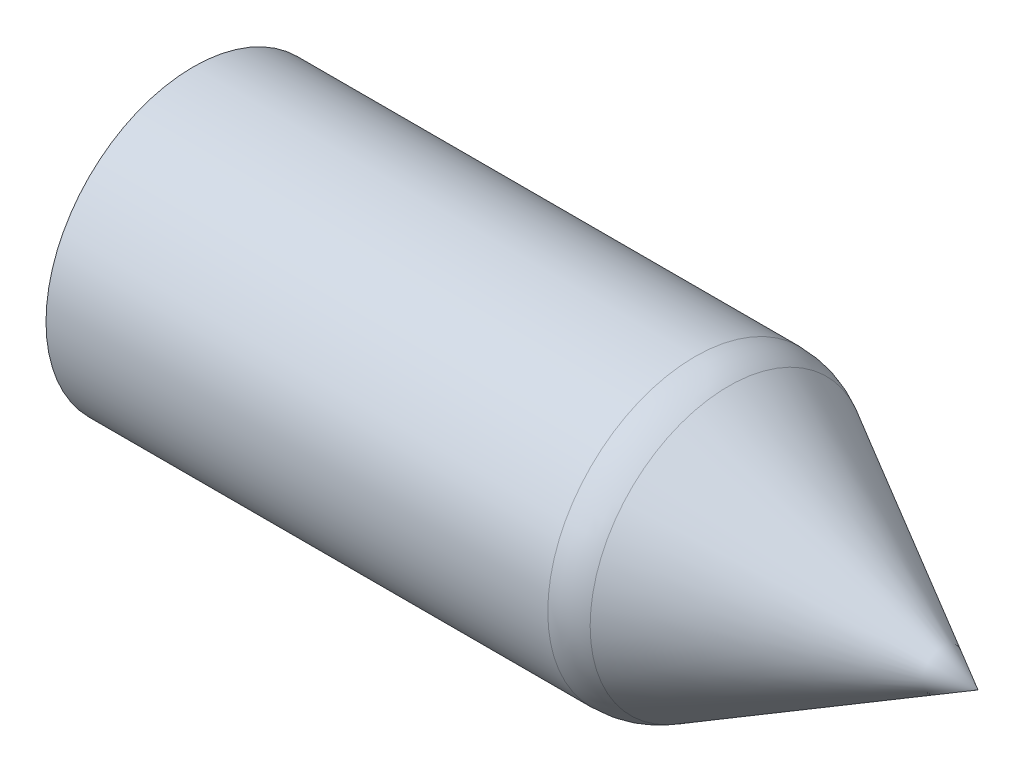
SolidWorks part; units mm, degrees
ref_plane "Ebene vorne" through (0, 0, 0) normal (0, 0, 1) x (1, 0, 0)
ref_plane "Ebene oben" through (0, 0, 0) normal (0, 1, 0) x (1, 0, 0)
ref_plane "Ebene rechts" through (0, 0, 0) normal (1, 0, 0) x (0, 0, -1)
sketch "Skizze1" plane through (0, 0, 0) normal (0, 1, 0) x (1, 0, 0)
  line L0 (0, 0) -> (-68.7476, 0) construction
  line L1 (0, 0) -> (-7.6485, 4.25)
  line L2 (-7.6485, 4.25) -> (-22.6485, 4.25)
  line L3 (-22.6485, 4.25) -> (-22.6485, 0)
  line L4 (0, 0) -> (-22.6485, 0)
  dimension "D1" = 8.75
  dimension "D2" = 15
  dimension "D3" = 4.25
revolve "Rotation1" add sketch "Skizze1" angle 360 about L0
fillet "Verrundung1" radius 2 1 edges at (-7.6485, 0, -4.25)
